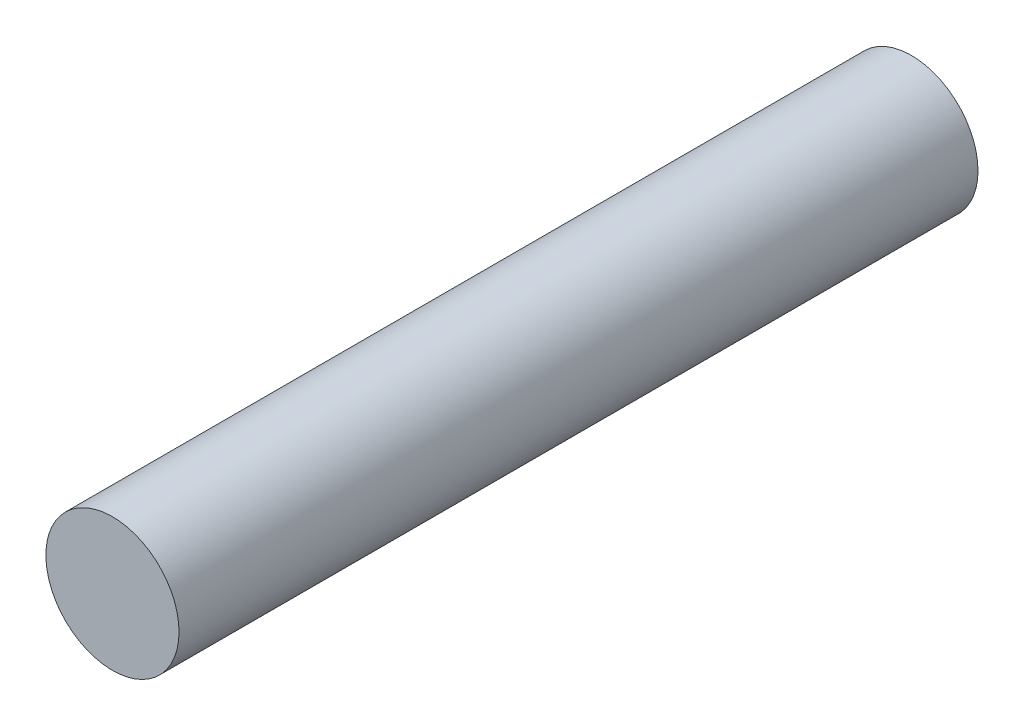
SolidWorks part; units mm, degrees
ref_plane "Front Plane" through (0, 0, 0) normal (0, 0, 1) x (1, 0, 0)
ref_plane "Top Plane" through (0, 0, 0) normal (0, 1, 0) x (1, 0, 0)
ref_plane "Right Plane" through (0, 0, 0) normal (1, 0, 0) x (0, 0, -1)
sketch "Sketch1" plane through (0, 0, 0) normal (0, 0, 1) x (1, 0, 0)
  circle A0 centre (0, 0) radius 0.5
  point P3 (0, 0)
  dimension "D1" = 1
extrude "Boss-Extrude1" add sketch "Sketch1" along normal blind 6
